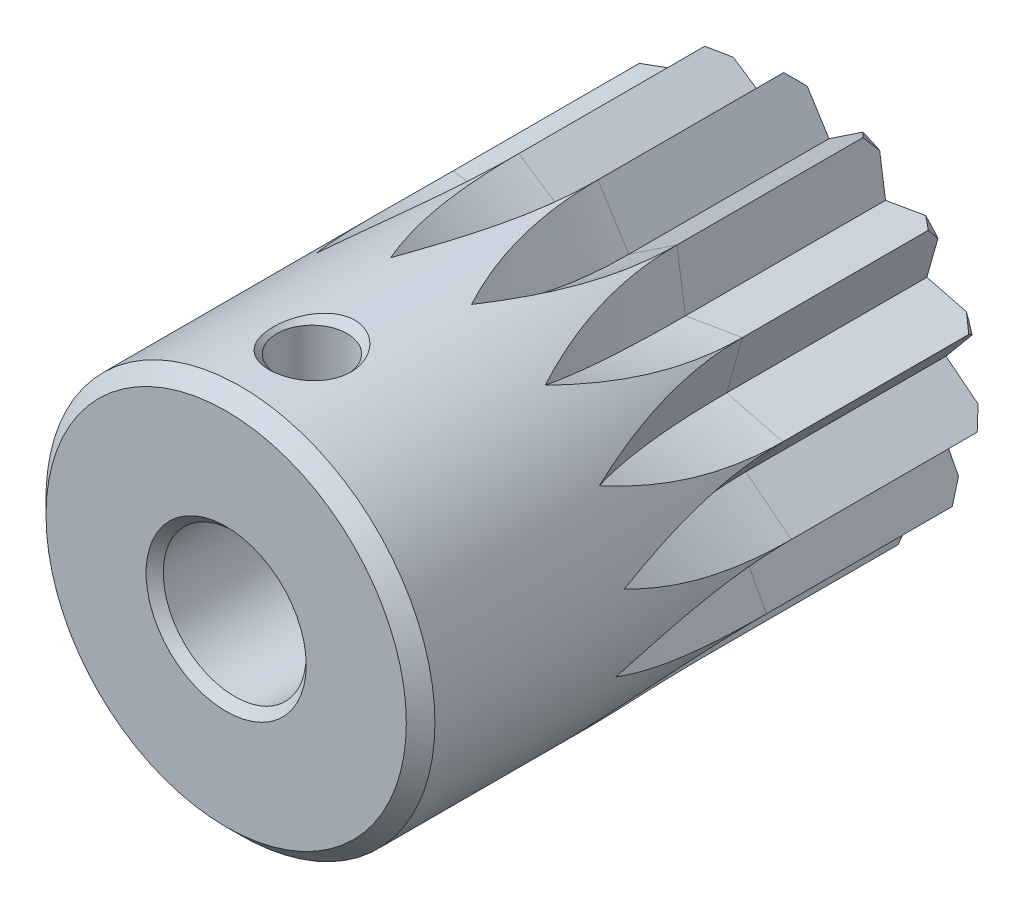
SolidWorks part; units mm, degrees
material "AISI 304"
ref_plane "Front Plane" through (0, 0, 0) normal (0, 0, 1) x (1, 0, 0)
ref_plane "Top Plane" through (0, 0, 0) normal (0, 1, 0) x (1, 0, 0)
ref_plane "Right Plane" through (0, 0, 0) normal (1, 0, 0) x (0, 0, -1)
ref_plane "Plane1" through (0, 0, 0) normal (1, 0, 0) x (0, 0, -1)
sketch "Sketch1" plane through (0, 0, 0) normal (1, 0, 0) x (0, 0, -1)
  line L0 (-20, 2.8) -> (-19.7, 2.5)
  line L1 (-19.7, 2.5) -> (-0.3, 2.5)
  line L2 (-0.3, 2.5) -> (0, 2.8)
  line L3 (0, 2.8) -> (0, 6.3)
  line L4 (0, 6.3) -> (-0.5, 6.8)
  line L5 (-0.5, 6.8) -> (-19.5, 6.8)
  line L6 (-19.5, 6.8) -> (-20, 6.3)
  line L7 (-20, 6.3) -> (-20, 2.8)
  line L8 (0, 0) -> (-20, 0) construction
revolve "Revolve1" add sketch "Sketch1" angle 360 about L8
ref_plane "Plane2" through (0, 0, 7) normal (0, 0, 1) x (1, 0, 0)
sketch "Sketch2" plane through (0, 0, 7) normal (0, 0, 1) x (1, 0, 0)
  line L0 (-6.7627, -0.7108) -> (-4.9455, -1.6069)
  line L1 (-4.9455, -1.6069) -> (-5.889, -3.4)
  line L2 (-5.889, -3.4) -> (-3.8644, -3.4795)
  line L3 (-3.8644, -3.4795) -> (-3.9969, -5.5013)
  line L4 (-3.9969, -5.5013) -> (-2.115, -4.7504)
  line L5 (-2.115, -4.7504) -> (-1.4138, -6.6514)
  line L6 (-1.4138, -6.6514) -> (0, -5.2)
  line L7 (0, -5.2) -> (1.4138, -6.6514)
  line L8 (1.4138, -6.6514) -> (2.115, -4.7504)
  line L9 (2.115, -4.7504) -> (3.9969, -5.5013)
  line L10 (3.9969, -5.5013) -> (3.8644, -3.4795)
  line L11 (3.8644, -3.4795) -> (5.889, -3.4)
  line L12 (5.889, -3.4) -> (4.9455, -1.6069)
  line L13 (4.9455, -1.6069) -> (6.7627, -0.7108)
  line L14 (6.7627, -0.7108) -> (5.1715, 0.5435)
  line L15 (5.1715, 0.5435) -> (6.4672, 2.1013)
  line L16 (6.4672, 2.1013) -> (4.5033, 2.6)
  line L17 (4.5033, 2.6) -> (5.0534, 4.5501)
  line L18 (5.0534, 4.5501) -> (3.0565, 4.2069)
  line L19 (3.0565, 4.2069) -> (2.7658, 6.2121)
  line L20 (2.7658, 6.2121) -> (1.0811, 5.0864)
  line L21 (1.0811, 5.0864) -> (0, 6.8)
  line L22 (0, 6.8) -> (-1.0811, 5.0864)
  line L23 (-1.0811, 5.0864) -> (-2.7658, 6.2121)
  line L24 (-2.7658, 6.2121) -> (-3.0565, 4.2069)
  line L25 (-3.0565, 4.2069) -> (-5.0534, 4.5501)
  line L26 (-5.0534, 4.5501) -> (-4.5033, 2.6)
  line L27 (-4.5033, 2.6) -> (-6.4672, 2.1013)
  line L28 (-6.4672, 2.1013) -> (-5.1715, 0.5435)
  line L29 (-5.1715, 0.5435) -> (-6.7627, -0.7108)
  circle A0 centre (0, 0) radius 13.6
extrude "Cut-Extrude1" cut sketch "Sketch2" against normal blind 7
ref_plane "Plane3" through (0, 0, 7) normal (0, 0, 1) x (1, 0, 0)
sketch "Sketch3" plane through (0, 0, 7) normal (0, 0, 1) x (1, 0, 0)
  line L0 (-2.0791, 16.5815) -> (0, 6.8)
  line L1 (0, 6.8) -> (-1.0811, 5.0864)
  line L2 (-1.0811, 5.0864) -> (-2.7658, 6.2121)
  line L3 (-2.7658, 6.2121) -> (-4.8449, 15.9936)
  line L4 (-4.8449, 15.9936) -> (-2.0791, 16.5815)
  line L5 (-4.8449, 15.9936) -> (-2.0791, 16.5815) construction
revolve "Cut-Revolve1" cut sketch "Sketch3" angle 360 about L5
ref_plane "Plane4" through (0, 0, 7) normal (0, 0, 1) x (1, 0, 0)
sketch "Sketch4" plane through (0, 0, 7) normal (0, 0, 1) x (1, 0, 0)
  line L0 (4.8449, 15.9936) -> (2.7658, 6.2121)
  line L1 (2.7658, 6.2121) -> (1.0811, 5.0864)
  line L2 (1.0811, 5.0864) -> (0, 6.8)
  line L3 (0, 6.8) -> (2.0791, 16.5815)
  line L4 (2.0791, 16.5815) -> (4.8449, 15.9936)
  line L5 (2.0791, 16.5815) -> (4.8449, 15.9936) construction
revolve "Cut-Revolve2" cut sketch "Sketch4" angle 360 about L5
ref_plane "Plane5" through (0, 0, 7) normal (0, 0, 1) x (1, 0, 0)
sketch "Sketch5" plane through (0, 0, 7) normal (0, 0, 1) x (1, 0, 0)
  line L0 (10.9312, 12.6403) -> (5.0534, 4.5501)
  line L1 (5.0534, 4.5501) -> (3.0565, 4.2069)
  line L2 (3.0565, 4.2069) -> (2.7658, 6.2121)
  line L3 (2.7658, 6.2121) -> (8.6437, 14.3023)
  line L4 (8.6437, 14.3023) -> (10.9312, 12.6403)
  line L5 (8.6437, 14.3023) -> (10.9312, 12.6403) construction
revolve "Cut-Revolve3" cut sketch "Sketch5" angle 360 about L5
ref_plane "Plane6" through (0, 0, 7) normal (0, 0, 1) x (1, 0, 0)
sketch "Sketch6" plane through (0, 0, 7) normal (0, 0, 1) x (1, 0, 0)
  line L0 (15.1274, 7.1013) -> (6.4672, 2.1013)
  line L1 (6.4672, 2.1013) -> (4.5033, 2.6)
  line L2 (4.5033, 2.6) -> (5.0534, 4.5501)
  line L3 (5.0534, 4.5501) -> (13.7136, 9.5501)
  line L4 (13.7136, 9.5501) -> (15.1274, 7.1013)
  line L5 (13.7136, 9.5501) -> (15.1274, 7.1013) construction
revolve "Cut-Revolve4" cut sketch "Sketch6" angle 360 about L5
ref_plane "Plane7" through (0, 0, 7) normal (0, 0, 1) x (1, 0, 0)
sketch "Sketch7" plane through (0, 0, 7) normal (0, 0, 1) x (1, 0, 0)
  line L0 (16.708, 0.3345) -> (6.7627, -0.7108)
  line L1 (6.7627, -0.7108) -> (5.1715, 0.5435)
  line L2 (5.1715, 0.5435) -> (6.4672, 2.1013)
  line L3 (6.4672, 2.1013) -> (16.4124, 3.1466)
  line L4 (16.4124, 3.1466) -> (16.708, 0.3345)
  line L5 (16.4124, 3.1466) -> (16.708, 0.3345) construction
revolve "Cut-Revolve5" cut sketch "Sketch7" angle 360 about L5
ref_plane "Plane8" through (0, 0, 7) normal (0, 0, 1) x (1, 0, 0)
sketch "Sketch8" plane through (0, 0, 7) normal (0, 0, 1) x (1, 0, 0)
  line L0 (15.3995, -6.4902) -> (5.889, -3.4)
  line L1 (5.889, -3.4) -> (4.9455, -1.6069)
  line L2 (4.9455, -1.6069) -> (6.7627, -0.7108)
  line L3 (6.7627, -0.7108) -> (16.2733, -3.801)
  line L4 (16.2733, -3.801) -> (15.3995, -6.4902)
  line L5 (16.2733, -3.801) -> (15.3995, -6.4902) construction
revolve "Cut-Revolve6" cut sketch "Sketch8" angle 360 about L5
ref_plane "Plane9" through (0, 0, 7) normal (0, 0, 1) x (1, 0, 0)
sketch "Sketch9" plane through (0, 0, 7) normal (0, 0, 1) x (1, 0, 0)
  line L0 (11.4284, -12.1926) -> (3.9969, -5.5013)
  line L1 (3.9969, -5.5013) -> (3.8644, -3.4795)
  line L2 (3.8644, -3.4795) -> (5.889, -3.4)
  line L3 (5.889, -3.4) -> (13.3204, -10.0913)
  line L4 (13.3204, -10.0913) -> (11.4284, -12.1926)
  line L5 (13.3204, -10.0913) -> (11.4284, -12.1926) construction
revolve "Cut-Revolve7" cut sketch "Sketch9" angle 360 about L5
ref_plane "Plane10" through (0, 0, 7) normal (0, 0, 1) x (1, 0, 0)
sketch "Sketch10" plane through (0, 0, 7) normal (0, 0, 1) x (1, 0, 0)
  line L0 (5.4812, -15.7869) -> (1.4138, -6.6514)
  line L1 (1.4138, -6.6514) -> (2.115, -4.7504)
  line L2 (2.115, -4.7504) -> (3.9969, -5.5013)
  line L3 (3.9969, -5.5013) -> (8.0643, -14.6368)
  line L4 (8.0643, -14.6368) -> (5.4812, -15.7869)
  line L5 (8.0643, -14.6368) -> (5.4812, -15.7869) construction
revolve "Cut-Revolve8" cut sketch "Sketch10" angle 360 about L5
ref_plane "Plane11" through (0, 0, 7) normal (0, 0, 1) x (1, 0, 0)
sketch "Sketch11" plane through (0, 0, 7) normal (0, 0, 1) x (1, 0, 0)
  line L0 (-1.4138, -16.6514) -> (-1.4138, -6.6514)
  line L1 (-1.4138, -6.6514) -> (0, -5.2)
  line L2 (0, -5.2) -> (1.4138, -6.6514)
  line L3 (1.4138, -6.6514) -> (1.4138, -16.6514)
  line L4 (1.4138, -16.6514) -> (-1.4138, -16.6514)
  line L5 (1.4138, -16.6514) -> (-1.4138, -16.6514) construction
revolve "Cut-Revolve9" cut sketch "Sketch11" angle 360 about L5
ref_plane "Plane12" through (0, 0, 7) normal (0, 0, 1) x (1, 0, 0)
sketch "Sketch12" plane through (0, 0, 7) normal (0, 0, 1) x (1, 0, 0)
  line L0 (-8.0643, -14.6368) -> (-3.9969, -5.5013)
  line L1 (-3.9969, -5.5013) -> (-2.115, -4.7504)
  line L2 (-2.115, -4.7504) -> (-1.4138, -6.6514)
  line L3 (-1.4138, -6.6514) -> (-5.4812, -15.7869)
  line L4 (-5.4812, -15.7869) -> (-8.0643, -14.6368)
  line L5 (-5.4812, -15.7869) -> (-8.0643, -14.6368) construction
revolve "Cut-Revolve10" cut sketch "Sketch12" angle 360 about L5
ref_plane "Plane13" through (0, 0, 7) normal (0, 0, 1) x (1, 0, 0)
sketch "Sketch13" plane through (0, 0, 7) normal (0, 0, 1) x (1, 0, 0)
  line L0 (-13.3204, -10.0913) -> (-5.889, -3.4)
  line L1 (-5.889, -3.4) -> (-3.8644, -3.4795)
  line L2 (-3.8644, -3.4795) -> (-3.9969, -5.5013)
  line L3 (-3.9969, -5.5013) -> (-11.4284, -12.1926)
  line L4 (-11.4284, -12.1926) -> (-13.3204, -10.0913)
  line L5 (-11.4284, -12.1926) -> (-13.3204, -10.0913) construction
revolve "Cut-Revolve11" cut sketch "Sketch13" angle 360 about L5
ref_plane "Plane14" through (0, 0, 7) normal (0, 0, 1) x (1, 0, 0)
sketch "Sketch14" plane through (0, 0, 7) normal (0, 0, 1) x (1, 0, 0)
  line L0 (-16.2733, -3.801) -> (-6.7627, -0.7108)
  line L1 (-6.7627, -0.7108) -> (-4.9455, -1.6069)
  line L2 (-4.9455, -1.6069) -> (-5.889, -3.4)
  line L3 (-5.889, -3.4) -> (-15.3995, -6.4902)
  line L4 (-15.3995, -6.4902) -> (-16.2733, -3.801)
  line L5 (-15.3995, -6.4902) -> (-16.2733, -3.801) construction
revolve "Cut-Revolve12" cut sketch "Sketch14" angle 360 about L5
ref_plane "Plane15" through (0, 0, 7) normal (0, 0, 1) x (1, 0, 0)
sketch "Sketch15" plane through (0, 0, 7) normal (0, 0, 1) x (1, 0, 0)
  line L0 (-16.4124, 3.1466) -> (-6.4672, 2.1013)
  line L1 (-6.4672, 2.1013) -> (-5.1715, 0.5435)
  line L2 (-5.1715, 0.5435) -> (-6.7627, -0.7108)
  line L3 (-6.7627, -0.7108) -> (-16.708, 0.3345)
  line L4 (-16.708, 0.3345) -> (-16.4124, 3.1466)
  line L5 (-16.708, 0.3345) -> (-16.4124, 3.1466) construction
revolve "Cut-Revolve13" cut sketch "Sketch15" angle 360 about L5
ref_plane "Plane16" through (0, 0, 7) normal (0, 0, 1) x (1, 0, 0)
sketch "Sketch16" plane through (0, 0, 7) normal (0, 0, 1) x (1, 0, 0)
  line L0 (-13.7136, 9.5501) -> (-5.0534, 4.5501)
  line L1 (-5.0534, 4.5501) -> (-4.5033, 2.6)
  line L2 (-4.5033, 2.6) -> (-6.4672, 2.1013)
  line L3 (-6.4672, 2.1013) -> (-15.1274, 7.1013)
  line L4 (-15.1274, 7.1013) -> (-13.7136, 9.5501)
  line L5 (-15.1274, 7.1013) -> (-13.7136, 9.5501) construction
revolve "Cut-Revolve14" cut sketch "Sketch16" angle 360 about L5
ref_plane "Plane17" through (0, 0, 7) normal (0, 0, 1) x (1, 0, 0)
sketch "Sketch17" plane through (0, 0, 7) normal (0, 0, 1) x (1, 0, 0)
  line L0 (-8.6437, 14.3023) -> (-2.7658, 6.2121)
  line L1 (-2.7658, 6.2121) -> (-3.0565, 4.2069)
  line L2 (-3.0565, 4.2069) -> (-5.0534, 4.5501)
  line L3 (-5.0534, 4.5501) -> (-10.9312, 12.6403)
  line L4 (-10.9312, 12.6403) -> (-8.6437, 14.3023)
  line L5 (-10.9312, 12.6403) -> (-8.6437, 14.3023) construction
revolve "Cut-Revolve15" cut sketch "Sketch17" angle 360 about L5
ref_plane "Plane18" through (0, 0, 17) normal (0, 0, 1) x (1, 0, 0)
sketch "Sketch18" plane through (0, 0, 17) normal (0, 0, 1) x (1, 0, 0)
  line L0 (0, 1.5) -> (-1.2295, 1.5)
  line L1 (-1.2295, 1.5) -> (-1.2295, 6.5295)
  line L2 (-1.2295, 6.5295) -> (-1.5, 6.8)
  line L3 (-1.5, 6.8) -> (-1.5, 7.8)
  line L4 (-1.5, 7.8) -> (0, 7.8)
  line L5 (0, 7.8) -> (0, 1.5)
  line L6 (0, 7.8) -> (0, 1.5) construction
revolve "Cut-Revolve16" cut sketch "Sketch18" angle 360 about L6
